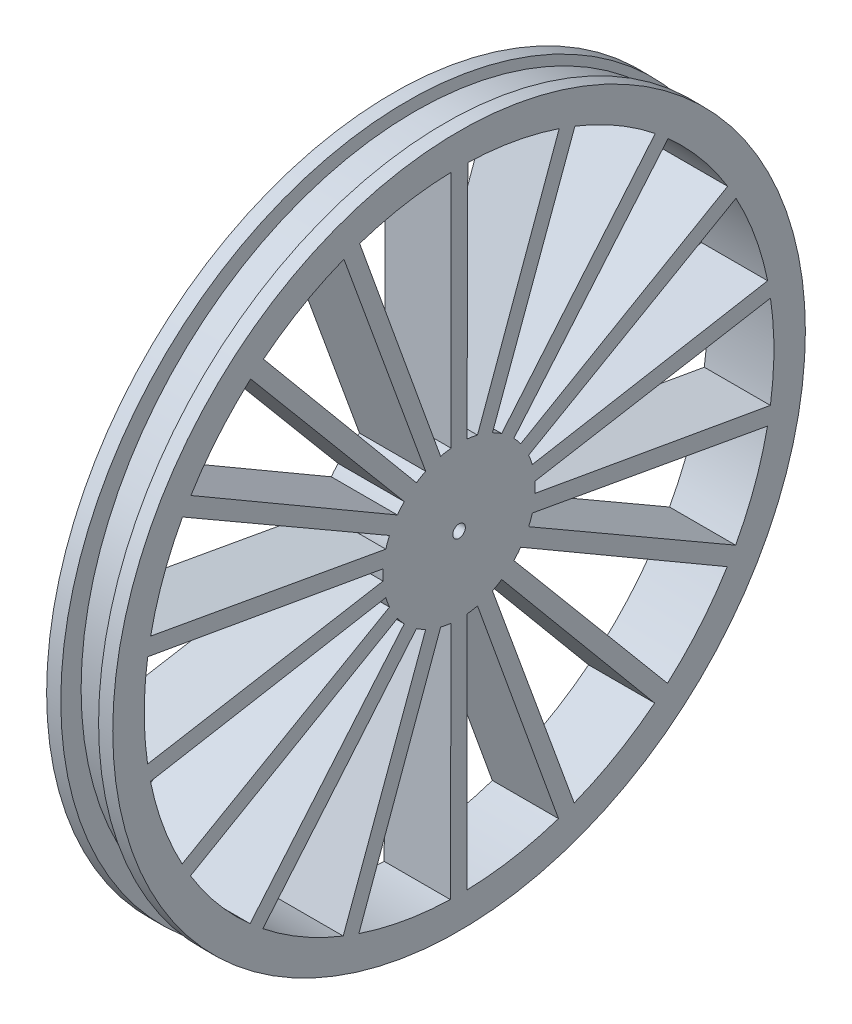
SolidWorks part; units mm, degrees
ref_plane "Front Plane" through (0, 0, 0) normal (0, 0, 1) x (1, 0, 0)
ref_plane "Top Plane" through (0, 0, 0) normal (0, 1, 0) x (1, 0, 0)
ref_plane "Right Plane" through (0, 0, 0) normal (1, 0, 0) x (0, 0, -1)
sketch "Sketch3" plane through (0, 0, 0) normal (1, 0, 0) x (0, 0, -1)
  line L0 (2.9273, 11.7406) -> (15.907, 47.4022)
  line L1 (5.3043, 10.8754) -> (18.3986, 46.4918)
  line L2 (6.7662, 10.0314) -> (31.1602, 39.103)
  line L3 (0, 8.1) -> (-0.5862, 5.5772)
  line L4 (0, 8.1) -> (0.5862, 5.5772)
  line L5 (1.6841, 7.923) -> (0.5862, 5.5772)
  line L6 (1.6841, 7.923) -> (1.733, 5.3335)
  line L7 (3.2946, 7.3997) -> (1.733, 5.3335)
  line L8 (3.2946, 7.3997) -> (2.804, 4.8566)
  line L9 (4.7611, 6.553) -> (2.804, 4.8566)
  line L10 (4.7611, 6.553) -> (3.7525, 4.1675)
  line L11 (6.0195, 5.42) -> (3.7525, 4.1675)
  line L12 (6.0195, 5.42) -> (4.5369, 3.2963)
  line L13 (7.0148, 4.05) -> (4.5369, 3.2963)
  line L14 (7.0148, 4.05) -> (5.1231, 2.281)
  line L15 (7.7036, 2.503) -> (5.1231, 2.281)
  line L16 (7.7036, 2.503) -> (5.4854, 1.166)
  line L17 (8.0556, 0.8467) -> (5.4854, 1.166)
  line L18 (8.0556, 0.8467) -> (5.608, 0)
  line L19 (8.0556, -0.8467) -> (5.608, 0)
  line L20 (8.0556, -0.8467) -> (5.4854, -1.166)
  line L21 (7.7036, -2.503) -> (5.4854, -1.166)
  line L22 (7.7036, -2.503) -> (5.1231, -2.281)
  line L23 (7.0148, -4.05) -> (5.1231, -2.281)
  line L24 (7.0148, -4.05) -> (4.5369, -3.2963)
  line L25 (6.0195, -5.42) -> (4.5369, -3.2963)
  line L26 (6.0195, -5.42) -> (3.7525, -4.1675)
  line L27 (4.7611, -6.553) -> (3.7525, -4.1675)
  line L28 (4.7611, -6.553) -> (2.804, -4.8566)
  line L29 (3.2946, -7.3997) -> (2.804, -4.8566)
  line L30 (3.2946, -7.3997) -> (1.733, -5.3335)
  line L31 (1.6841, -7.923) -> (1.733, -5.3335)
  line L32 (1.6841, -7.923) -> (0.5862, -5.5772)
  line L33 (0, -8.1) -> (0.5862, -5.5772)
  line L34 (0, -8.1) -> (-0.5862, -5.5772)
  line L35 (-1.6841, -7.923) -> (-0.5862, -5.5772)
  line L36 (-1.6841, -7.923) -> (-1.733, -5.3335)
  line L37 (-3.2946, -7.3997) -> (-1.733, -5.3335)
  line L38 (-3.2946, -7.3997) -> (-2.804, -4.8566)
  line L39 (-4.7611, -6.553) -> (-2.804, -4.8566)
  line L40 (-4.7611, -6.553) -> (-3.7525, -4.1675)
  line L41 (-6.0195, -5.42) -> (-3.7525, -4.1675)
  line L42 (-6.0195, -5.42) -> (-4.5369, -3.2963)
  line L43 (-7.0148, -4.05) -> (-4.5369, -3.2963)
  line L44 (-7.0148, -4.05) -> (-5.1231, -2.281)
  line L45 (-7.7036, -2.503) -> (-5.1231, -2.281)
  line L46 (-7.7036, -2.503) -> (-5.4854, -1.166)
  line L47 (-8.0556, -0.8467) -> (-5.4854, -1.166)
  line L48 (-8.0556, -0.8467) -> (-5.608, 0)
  line L49 (-8.0556, 0.8467) -> (-5.608, 0)
  line L50 (-8.0556, 0.8467) -> (-5.4854, 1.166)
  line L51 (-7.7036, 2.503) -> (-5.4854, 1.166)
  line L52 (-7.7036, 2.503) -> (-5.1231, 2.281)
  line L53 (-7.0148, 4.05) -> (-5.1231, 2.281)
  line L54 (-7.0148, 4.05) -> (-4.5369, 3.2963)
  line L55 (-6.0195, 5.42) -> (-4.5369, 3.2963)
  line L56 (-6.0195, 5.42) -> (-3.7525, 4.1675)
  line L57 (-4.7611, 6.553) -> (-3.7525, 4.1675)
  line L58 (-4.7611, 6.553) -> (-2.804, 4.8566)
  line L59 (-3.2946, 7.3997) -> (-2.804, 4.8566)
  line L60 (-3.2946, 7.3997) -> (-1.733, 5.3335)
  line L61 (-1.6841, 7.923) -> (-1.733, 5.3335)
  line L62 (-1.6841, 7.923) -> (-0.5862, 5.5772)
  line L63 (-1.2648, 12.0337) -> (-1.2648, 49.984)
  line L64 (1.2648, 12.0337) -> (1.3879, 49.9807)
  line L71 (-1.2648, -12.0337) -> (0.8153, 7.7573) construction
  line L72 (0, -8.1) -> (0, 7.8) construction
  line L73 (1.2648, -12.0337) -> (-0.8153, 7.7573) construction
  line L74 (8.704, 8.4054) -> (33.1902, 37.3953)
  line L75 (9.7891, 7.1122) -> (42.655, 26.0873)
  line L76 (11.0539, 4.9215) -> (43.9785, 23.7884)
  line L77 (11.6313, 3.3352) -> (49.005, 9.9252)
  line L78 (12.0705, 0.8441) -> (49.4624, 7.3122)
  line L79 (12.0705, -0.8441) -> (49.4443, -7.4341)
  line L80 (11.6313, -3.3352) -> (48.9804, -10.0459)
  line L81 (11.0539, -4.9215) -> (43.9198, -23.8967)
  line L82 (9.7891, -7.1122) -> (42.5906, -26.1923)
  line L83 (8.704, -8.4054) -> (33.098, -37.477)
  line L84 (6.7662, -10.0314) -> (31.0638, -39.1796)
  line L85 (5.3043, -10.8754) -> (18.2841, -46.537)
  line L86 (2.9273, -11.7406) -> (15.7902, -47.4412)
  line L87 (1.2648, -12.0337) -> (1.2648, -49.984)
  line L88 (-1.2648, -12.0337) -> (-1.3879, -49.9807)
  line L89 (-2.9273, -11.7406) -> (-15.907, -47.4022)
  line L90 (-5.3043, -10.8754) -> (-18.3986, -46.4918)
  line L91 (-6.7662, -10.0314) -> (-31.1602, -39.103)
  line L92 (-8.704, -8.4054) -> (-33.1902, -37.3953)
  line L93 (-9.7891, -7.1122) -> (-42.655, -26.0873)
  line L94 (-11.0539, -4.9215) -> (-43.9785, -23.7884)
  line L95 (-11.6313, -3.3352) -> (-49.005, -9.9252)
  line L96 (-12.0705, -0.8441) -> (-49.4624, -7.3122)
  line L97 (-12.0705, 0.8441) -> (-49.4443, 7.4341)
  line L98 (-11.6313, 3.3352) -> (-48.9804, 10.0459)
  line L99 (-11.0539, 4.9215) -> (-43.9198, 23.8967)
  line L100 (-9.7891, 7.1122) -> (-42.5906, 26.1923)
  line L101 (-8.704, 8.4054) -> (-33.098, 37.477)
  line L102 (-6.7662, 10.0314) -> (-31.0638, 39.1796)
  line L103 (-5.3043, 10.8754) -> (-18.2841, 46.537)
  line L104 (-2.9273, 11.7406) -> (-15.7902, 47.4412)
  circle A0 centre (0, 0) radius 8.1 construction
  arc A1 (-1.2648, 12.0337) -> (-2.9273, 11.7406) centre (0, 0) ccw
  circle A2 centre (0, 0) radius 55
  circle A4 centre (0, 0) radius 5.6 construction
  arc A5 (49.9807, 1.3879) -> (49.4624, 7.3122) centre (0, 0) ccw
  circle A6 centre (0, 0) radius 12.1 construction
  arc A7 (11.6313, 3.3352) -> (11.0539, 4.9215) centre (0, 0) ccw
  arc A10 (-11.6313, -3.3352) -> (-11.0539, -4.9215) centre (0, 0) ccw
  arc A12 (1.2648, -12.0337) -> (2.9273, -11.7406) centre (0, 0) ccw
  arc A13 (-1.2648, 49.984) -> (-15.7902, 47.4412) centre (0, 0) ccw
  arc A14 (-49.9807, -1.3879) -> (-49.4624, -7.3122) centre (0, 0) ccw
  arc A15 (-11.0539, 4.9215) -> (-11.6313, 3.3352) centre (0, 0) ccw
  arc A16 (-33.098, 37.477) -> (-42.5906, 26.1923) centre (0, 0) ccw
  arc A17 (-33.098, 37.477) -> (-42.5906, 26.1923) centre (0, 0) ccw
  arc A18 (-18.2841, 46.537) -> (-31.0638, 39.1796) centre (0, 0) ccw
  arc A19 (-18.2841, 46.537) -> (-31.0638, 39.1796) centre (0, 0) ccw
  arc A20 (-1.2648, 49.984) -> (-15.7902, 47.4412) centre (0, 0) ccw
  arc A21 (15.907, 47.4022) -> (1.3879, 49.9807) centre (0, 0) ccw
  arc A22 (15.907, 47.4022) -> (1.3879, 49.9807) centre (0, 0) ccw
  arc A23 (31.1602, 39.103) -> (18.3986, 46.4918) centre (0, 0) ccw
  arc A24 (31.1602, 39.103) -> (18.3986, 46.4918) centre (0, 0) ccw
  arc A25 (49.005, 9.9252) -> (33.1902, 37.3953) centre (0, 0) ccw
  arc A26 (49.005, 9.9252) -> (33.1902, 37.3953) centre (0, 0) ccw
  arc A27 (49.4443, -7.4341) -> (49.4624, 7.3122) centre (0, 0) ccw
  arc A28 (49.4443, -7.4341) -> (49.9807, -1.3879) centre (0, 0) ccw
  arc A29 (43.9198, -23.8967) -> (48.9804, -10.0459) centre (0, 0) ccw
  arc A30 (43.9198, -23.8967) -> (48.9804, -10.0459) centre (0, 0) ccw
  arc A31 (33.098, -37.477) -> (42.5906, -26.1923) centre (0, 0) ccw
  arc A32 (33.098, -37.477) -> (42.5906, -26.1923) centre (0, 0) ccw
  arc A33 (18.2841, -46.537) -> (31.0638, -39.1796) centre (0, 0) ccw
  arc A34 (18.2841, -46.537) -> (31.0638, -39.1796) centre (0, 0) ccw
  arc A35 (1.2648, -49.984) -> (15.7902, -47.4412) centre (0, 0) ccw
  arc A36 (1.2648, -49.984) -> (15.7902, -47.4412) centre (0, 0) ccw
  arc A37 (-15.907, -47.4022) -> (-1.3879, -49.9807) centre (0, 0) ccw
  arc A38 (-15.907, -47.4022) -> (-1.3879, -49.9807) centre (0, 0) ccw
  arc A39 (-31.1602, -39.103) -> (-18.3986, -46.4918) centre (0, 0) ccw
  arc A40 (-31.1602, -39.103) -> (-18.3986, -46.4918) centre (0, 0) ccw
  arc A41 (-42.655, -26.0873) -> (-33.1902, -37.3953) centre (0, 0) ccw
  arc A42 (-42.655, -26.0873) -> (-33.1902, -37.3953) centre (0, 0) ccw
  arc A43 (-49.005, -9.9252) -> (-43.9785, -23.7884) centre (0, 0) ccw
  arc A44 (-49.005, -9.9252) -> (-43.9785, -23.7884) centre (0, 0) ccw
  arc A45 (-49.4443, 7.4341) -> (-49.4624, -7.3122) centre (0, 0) ccw
  arc A46 (-49.4443, 7.4341) -> (-49.9807, 1.3879) centre (0, 0) ccw
  arc A47 (-43.9198, 23.8967) -> (-48.9804, 10.0459) centre (0, 0) ccw
  arc A48 (-43.9198, 23.8967) -> (-48.9804, 10.0459) centre (0, 0) ccw
  arc A49 (-11.0539, 4.9215) -> (-11.6313, 3.3352) centre (0, 0) ccw
  arc A50 (-8.704, 8.4054) -> (-9.7891, 7.1122) centre (0, 0) ccw
  arc A51 (-8.704, 8.4054) -> (-9.7891, 7.1122) centre (0, 0) ccw
  arc A52 (-5.3043, 10.8754) -> (-6.7662, 10.0314) centre (0, 0) ccw
  arc A53 (-5.3043, 10.8754) -> (-6.7662, 10.0314) centre (0, 0) ccw
  arc A54 (-1.2648, 12.0337) -> (-2.9273, 11.7406) centre (0, 0) ccw
  arc A55 (2.9273, 11.7406) -> (1.2648, 12.0337) centre (0, 0) ccw
  arc A56 (2.9273, 11.7406) -> (1.2648, 12.0337) centre (0, 0) ccw
  arc A57 (6.7662, 10.0314) -> (5.3043, 10.8754) centre (0, 0) ccw
  arc A58 (6.7662, 10.0314) -> (5.3043, 10.8754) centre (0, 0) ccw
  arc A59 (9.7891, 7.1122) -> (8.704, 8.4054) centre (0, 0) ccw
  arc A60 (9.7891, 7.1122) -> (8.704, 8.4054) centre (0, 0) ccw
  arc A61 (11.6313, 3.3352) -> (11.0539, 4.9215) centre (0, 0) ccw
  arc A62 (12.0705, -0.8441) -> (12.0705, 0.8441) centre (0, 0) ccw
  arc A63 (11.0539, -4.9215) -> (11.6313, -3.3352) centre (0, 0) ccw
  arc A64 (11.0539, -4.9215) -> (11.6313, -3.3352) centre (0, 0) ccw
  arc A65 (8.704, -8.4054) -> (9.7891, -7.1122) centre (0, 0) ccw
  arc A66 (8.704, -8.4054) -> (9.7891, -7.1122) centre (0, 0) ccw
  arc A67 (5.3043, -10.8754) -> (6.7662, -10.0314) centre (0, 0) ccw
  arc A68 (5.3043, -10.8754) -> (6.7662, -10.0314) centre (0, 0) ccw
  arc A69 (1.2648, -12.0337) -> (2.9273, -11.7406) centre (0, 0) ccw
  arc A70 (-2.9273, -11.7406) -> (-1.2648, -12.0337) centre (0, 0) ccw
  arc A71 (-2.9273, -11.7406) -> (-1.2648, -12.0337) centre (0, 0) ccw
  arc A72 (-6.7662, -10.0314) -> (-5.3043, -10.8754) centre (0, 0) ccw
  arc A73 (-6.7662, -10.0314) -> (-5.3043, -10.8754) centre (0, 0) ccw
  arc A74 (-9.7891, -7.1122) -> (-8.704, -8.4054) centre (0, 0) ccw
  arc A75 (-9.7891, -7.1122) -> (-8.704, -8.4054) centre (0, 0) ccw
  arc A76 (-11.6313, -3.3352) -> (-11.0539, -4.9215) centre (0, 0) ccw
  arc A77 (-12.0337, 1.2648) -> (-12.0705, -0.8441) centre (0, 0) ccw
  point P8 (0, 0)
  point P9 (0, 0)
  point P13 (0, 0)
  point P17 (0, 0)
  point P25 (-0.5862, 5.5772)
  point P79 (0, 0)
  point P105 (0, 0)
  point P160 (0, 0)
  dimension "D1" = 16.2
  dimension "D3" = 110
  dimension "D8" = 100
  dimension "D4" = 18
  dimension "D5" = 2.5
  dimension "D2" = 4
  dimension "D6" = 30
extrude "Boss-Extrude4" add sketch "Sketch3" along normal blind 7 contours A2 A47 L99 A15 L98 A43 L95 A10 L94 A35 L87 A12 L86 A13 L63 A1 L104 L61 L62 L3 L4 L5 L6 L7 L8 L9 L10 L11 L12 L13 L14 L15 L16 L17 L18 L19 L20 L21 L22 L23 L24 L25 L26 L27 L28 L29
sketch "Sketch4" plane through (7, 0, 0) normal (1, 0, 0) x (0, 0, -1)
  line L0 (-11.6313, 3.3352) -> (-48.9804, 10.0459) construction
  line L1 (-12.0705, 0.8441) -> (-49.4443, 7.4341) construction
  line L2 (-11.6313, 3.3352) -> (-48.9804, 10.0459)
  line L3 (-12.0705, 0.8441) -> (-49.4443, 7.4341)
  line L4 (-11.0539, 4.9215) -> (-43.9198, 23.8967) construction
  line L5 (-9.7891, 7.1122) -> (-42.5906, 26.1923) construction
  line L6 (-8.704, 8.4054) -> (-33.098, 37.477) construction
  line L7 (-6.7662, 10.0314) -> (-31.0638, 39.1796) construction
  line L8 (-5.3043, 10.8754) -> (-18.2841, 46.537) construction
  line L9 (-2.9273, 11.7406) -> (-15.7902, 47.4412) construction
  line L10 (-1.2648, 12.0337) -> (-1.2648, 49.984) construction
  line L11 (1.2648, 12.0337) -> (1.3879, 49.9807) construction
  line L12 (2.9273, 11.7406) -> (15.907, 47.4022) construction
  line L13 (5.3043, 10.8754) -> (18.3986, 46.4918) construction
  line L14 (6.7662, 10.0314) -> (31.1602, 39.103) construction
  line L15 (8.704, 8.4054) -> (33.1902, 37.3953) construction
  line L16 (9.7891, 7.1122) -> (42.655, 26.0873) construction
  line L17 (11.0539, 4.9215) -> (43.9785, 23.7884) construction
  line L18 (11.6313, 3.3352) -> (49.005, 9.9252) construction
  line L19 (12.0705, 0.8441) -> (49.4624, 7.3122) construction
  line L20 (12.0705, -0.8441) -> (49.4443, -7.4341) construction
  line L21 (11.6313, -3.3352) -> (48.9804, -10.0459) construction
  line L22 (11.0539, -4.9215) -> (43.9198, -23.8967) construction
  line L23 (9.7891, -7.1122) -> (42.5906, -26.1923) construction
  line L24 (8.704, -8.4054) -> (33.098, -37.477) construction
  line L25 (6.7662, -10.0314) -> (31.0638, -39.1796) construction
  line L26 (5.3043, -10.8754) -> (18.2841, -46.537) construction
  line L27 (2.9273, -11.7406) -> (15.7902, -47.4412) construction
  line L28 (1.2648, -12.0337) -> (1.2648, -49.984) construction
  line L29 (-1.2648, -12.0337) -> (-1.3879, -49.9807) construction
  line L30 (-2.9273, -11.7406) -> (-15.907, -47.4022) construction
  line L31 (-5.3043, -10.8754) -> (-18.3986, -46.4918) construction
  line L32 (-6.7662, -10.0314) -> (-31.1602, -39.103) construction
  line L33 (-8.704, -8.4054) -> (-33.1902, -37.3953) construction
  line L34 (-9.7891, -7.1122) -> (-42.655, -26.0873) construction
  line L35 (-11.0539, -4.9215) -> (-43.9785, -23.7884) construction
  line L36 (-11.6313, -3.3352) -> (-49.005, -9.9252) construction
  line L37 (-12.0705, -0.8441) -> (-49.4624, -7.3122) construction
  line L38 (-12.0705, -0.8441) -> (-49.4624, -7.3122)
  line L39 (-11.6313, -3.3352) -> (-49.005, -9.9252)
  line L40 (-11.0539, -4.9215) -> (-43.9785, -23.7884)
  line L41 (-9.7891, -7.1122) -> (-42.655, -26.0873)
  line L42 (-8.704, -8.4054) -> (-33.1902, -37.3953)
  line L43 (-6.7662, -10.0314) -> (-31.1602, -39.103)
  line L44 (-5.3043, -10.8754) -> (-18.3986, -46.4918)
  line L45 (-2.9273, -11.7406) -> (-15.907, -47.4022)
  line L46 (-1.2648, -12.0337) -> (-1.3879, -49.9807)
  line L47 (1.2648, -12.0337) -> (1.2648, -49.984)
  line L48 (2.9273, -11.7406) -> (15.7902, -47.4412)
  line L49 (5.3043, -10.8754) -> (18.2841, -46.537)
  line L50 (6.7662, -10.0314) -> (31.0638, -39.1796)
  line L51 (8.704, -8.4054) -> (33.098, -37.477)
  line L52 (9.7891, -7.1122) -> (42.5906, -26.1923)
  line L53 (11.0539, -4.9215) -> (43.9198, -23.8967)
  line L54 (11.6313, -3.3352) -> (48.9804, -10.0459)
  line L55 (12.0705, -0.8441) -> (49.4443, -7.4341)
  line L56 (12.0705, 0.8441) -> (49.4624, 7.3122)
  line L57 (11.6313, 3.3352) -> (49.005, 9.9252)
  line L58 (11.0539, 4.9215) -> (43.9785, 23.7884)
  line L59 (9.7891, 7.1122) -> (42.655, 26.0873)
  line L60 (8.704, 8.4054) -> (33.1902, 37.3953)
  line L61 (6.7662, 10.0314) -> (31.1602, 39.103)
  line L62 (5.3043, 10.8754) -> (18.3986, 46.4918)
  line L63 (2.9273, 11.7406) -> (15.907, 47.4022)
  line L64 (1.2648, 12.0337) -> (1.3879, 49.9807)
  line L65 (-1.2648, 12.0337) -> (-1.2648, 49.984)
  line L66 (-2.9273, 11.7406) -> (-15.7902, 47.4412)
  line L67 (-5.3043, 10.8754) -> (-18.2841, 46.537)
  line L68 (-6.7662, 10.0314) -> (-31.0638, 39.1796)
  line L69 (-8.704, 8.4054) -> (-33.098, 37.477)
  line L70 (-9.7891, 7.1122) -> (-42.5906, 26.1923)
  line L71 (-11.0539, 4.9215) -> (-43.9198, 23.8967)
  circle A0 centre (0, 0) radius 12.1
  circle A1 centre (0, 0) radius 1
  arc A2 (-43.9198, 23.8967) -> (-48.9804, 10.0459) centre (0, 0) ccw construction
  circle A3 centre (0, 0) radius 55
  circle A4 centre (0, 0) radius 55
  arc A5 (-33.098, 37.477) -> (-42.5906, 26.1923) centre (0, 0) ccw construction
  arc A6 (-18.2841, 46.537) -> (-31.0638, 39.1796) centre (0, 0) ccw construction
  arc A7 (-1.2648, 49.984) -> (-15.7902, 47.4412) centre (0, 0) ccw construction
  arc A8 (15.907, 47.4022) -> (1.3879, 49.9807) centre (0, 0) ccw construction
  arc A9 (31.1602, 39.103) -> (18.3986, 46.4918) centre (0, 0) ccw construction
  arc A10 (42.655, 26.0873) -> (33.1902, 37.3953) centre (0, 0) ccw construction
  arc A11 (49.005, 9.9252) -> (43.9785, 23.7884) centre (0, 0) ccw construction
  arc A12 (49.4443, -7.4341) -> (49.4624, 7.3122) centre (0, 0) ccw construction
  arc A13 (43.9198, -23.8967) -> (48.9804, -10.0459) centre (0, 0) ccw construction
  arc A14 (33.098, -37.477) -> (42.5906, -26.1923) centre (0, 0) ccw construction
  arc A15 (18.2841, -46.537) -> (31.0638, -39.1796) centre (0, 0) ccw construction
  arc A16 (1.2648, -49.984) -> (15.7902, -47.4412) centre (0, 0) ccw construction
  arc A17 (-15.907, -47.4022) -> (-1.3879, -49.9807) centre (0, 0) ccw construction
  arc A18 (-31.1602, -39.103) -> (-18.3986, -46.4918) centre (0, 0) ccw construction
  arc A19 (-42.655, -26.0873) -> (-33.1902, -37.3953) centre (0, 0) ccw construction
  arc A20 (-49.005, -9.9252) -> (-43.9785, -23.7884) centre (0, 0) ccw construction
  arc A21 (-49.4443, 7.4341) -> (-49.4624, -7.3122) centre (0, 0) ccw construction
  arc A22 (-49.4443, 7.4341) -> (-49.4624, -7.3122) centre (0, 0) ccw
  arc A23 (-49.005, -9.9252) -> (-43.9785, -23.7884) centre (0, 0) ccw
  arc A24 (-42.655, -26.0873) -> (-33.1902, -37.3953) centre (0, 0) ccw
  arc A25 (-31.1602, -39.103) -> (-18.3986, -46.4918) centre (0, 0) ccw
  arc A26 (-15.907, -47.4022) -> (-1.3879, -49.9807) centre (0, 0) ccw
  arc A27 (1.2648, -49.984) -> (15.7902, -47.4412) centre (0, 0) ccw
  arc A28 (18.2841, -46.537) -> (31.0638, -39.1796) centre (0, 0) ccw
  arc A29 (33.098, -37.477) -> (42.5906, -26.1923) centre (0, 0) ccw
  arc A30 (43.9198, -23.8967) -> (48.9804, -10.0459) centre (0, 0) ccw
  arc A31 (49.4443, -7.4341) -> (49.4624, 7.3122) centre (0, 0) ccw
  arc A32 (49.005, 9.9252) -> (43.9785, 23.7884) centre (0, 0) ccw
  arc A33 (42.655, 26.0873) -> (33.1902, 37.3953) centre (0, 0) ccw
  arc A34 (31.1602, 39.103) -> (18.3986, 46.4918) centre (0, 0) ccw
  arc A35 (15.907, 47.4022) -> (1.3879, 49.9807) centre (0, 0) ccw
  arc A36 (-1.2648, 49.984) -> (-15.7902, 47.4412) centre (0, 0) ccw
  arc A37 (-18.2841, 46.537) -> (-31.0638, 39.1796) centre (0, 0) ccw
  arc A38 (-33.098, 37.477) -> (-42.5906, 26.1923) centre (0, 0) ccw
  arc A39 (-43.9198, 23.8967) -> (-48.9804, 10.0459) centre (0, 0) ccw
  dimension "D1" = 2
  dimension "D2" = 0
extrude "Boss-Extrude6" add sketch "Sketch4" along normal blind 3.5 and the other way blind 1 contours A4 A39 L71 A0 L70 A38 L69 L68 A37 L67 L66 A36 L65 L64 A35 L63 L62 A34 L61 L60 A33 L59 L58 A32 L57 L56 A31 L55 L54 A30 L53 L52 A29 L51 L50 A28 L49 L48 A27 | A0 A1
sketch "Sketch5" plane through (0, -0.004, -1.2257) normal (0, -0.0032, -1) x (-1, 0, 0)
  line L0 (0, 55) -> (-10.5, 55) construction
  line L1 (0, 55) -> (-2.25, 55) construction
  line L2 (-5.25, 54.5) -> (-5.25, 53) construction
  line L3 (-8.25, 53) -> (-2.25, 53)
  line L4 (-2.25, 53) -> (-2.25, 55)
  line L5 (-8.25, 53) -> (-8.25, 55)
  line L6 (14.7164, 0) -> (-20.8346, 0) construction
  line L8 (-2.25, 55) -> (-2.25, 56.2366)
  line L9 (-2.25, 56.2366) -> (-8.25, 56.2366)
  line L10 (-8.25, 56.2366) -> (-8.25, 55)
  line L11 (-8.25, 55) -> (-10.5, 55) construction
  dimension "D1" = 1.5
  dimension "D2" = 3
revolve "Cut-Revolve1" cut sketch "Sketch5" angle 360 about L6
